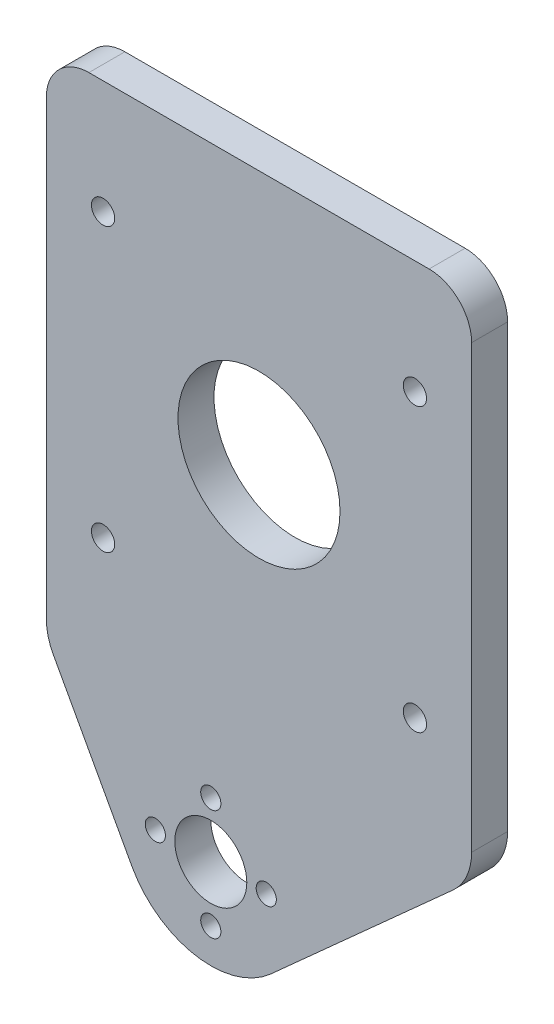
SolidWorks part; units mm, degrees
ref_plane "Front Plane" through (0, 0, 0) normal (0, 0, 1) x (1, 0, 0)
ref_plane "Top Plane" through (0, 0, 0) normal (0, 1, 0) x (1, 0, 0)
ref_plane "Right Plane" through (0, 0, 0) normal (1, 0, 0) x (0, 0, -1)
sketch "Sketch1" plane through (0, 0, 0) normal (0, 0, 1) x (1, 0, 0)
  line L1 (0, 0) -> (304.8, 0)
  line L2 (0, 0) -> (0, 89.8)
  line L3 (0, 89.8) -> (304.8, 89.8)
  line L4 (304.8, 0) -> (304.8, 89.8)
  circle A3 centre (152.4, 44.9) radius 14.2875
  point P7 (152.4, 44.9)
  circle B0 centre (109.4016, 62.8594) radius 2.54
  circle B1 centre (109.3994, 26.9384) radius 2.54
  circle B2 centre (73.4784, 26.9406) radius 2.54
  circle B3 centre (73.4806, 62.8616) radius 2.54
  circle B4 centre (91.44, 44.9) radius 17.145
  circle B5 centre (195.4006, 62.8616) radius 2.54
  circle B6 centre (231.3216, 62.8594) radius 2.54
  circle B7 centre (231.3194, 26.9384) radius 2.54
  circle B8 centre (195.3984, 26.9406) radius 2.54
  circle B9 centre (213.36, 44.9) radius 17.145
  dimension "D3" = 60.96
  dimension "D4" = 60.96
  dimension "D6" = 28.575
  dimension "D1" = 89.8
  dimension "D2" = 304.8
sketch_block_instance "Block1-1"
sketch_block "Block1" parameters "D1"=5.08, "D2"=34.29
sketch_block_instance "Block2-1"
sketch_block "Block2" parameters "D1"=5.08, "D2"=34.29
extrude "Boss-Extrude1" add sketch "Sketch1" along normal blind 6.35
sketch "Sketch2" plane through (0, 0, 6.35) normal (0, 0, 1) x (1, 0, 0)
  line L0 (304.8, 89.8) -> (0, 89.8) construction
  line L1 (114.9, 0) -> (189.9, 0)
  line L2 (114.9, 0) -> (114.9, 89.8)
  line L3 (114.9, 89.8) -> (189.9, 89.8)
  line L4 (189.9, 0) -> (189.9, 89.8)
  line L5 (114.9, 0) -> (189.9, 89.8) construction
  line L6 (114.9, 89.8) -> (189.9, 0) construction
  line L8 (114.9, 89.8) -> (-29.3949, 89.8)
  line L9 (114.9, 89.8) -> (114.9, -10.172)
  line L10 (114.9, -10.172) -> (-29.3949, -10.172)
  line L11 (-29.3949, 89.8) -> (-29.3949, -10.172)
  line L12 (189.9, 89.8) -> (343.3103, 89.8)
  line L13 (189.9, 89.8) -> (189.9, -29.3261)
  line L14 (189.9, -29.3261) -> (343.3103, -29.3261)
  line L15 (343.3103, 89.8) -> (343.3103, -29.3261)
  point P0 (152.4, 44.9)
  line M1 (0, 89.8) -> (0, 0)
  line M2 (0, 0) -> (304.8, 0)
  line M3 (304.8, 0) -> (304.8, 89.8)
  line M4 (304.8, 89.8) -> (0, 89.8)
  circle M6 centre (91.44, 44.9) radius 17.145
  circle M7 centre (109.4016, 62.8594) radius 2.54
  circle M8 centre (109.3994, 26.9384) radius 2.54
  circle M9 centre (73.4784, 26.9406) radius 2.54
  circle M10 centre (73.4806, 62.8616) radius 2.54
  circle M11 centre (213.36, 44.9) radius 17.145
  circle M12 centre (195.4006, 62.8616) radius 2.54
  circle M13 centre (231.3216, 62.8594) radius 2.54
  circle M14 centre (231.3194, 26.9384) radius 2.54
  circle M15 centre (195.3984, 26.9406) radius 2.54
  dimension "D1" = 75
extrude "Cut-Extrude1" cut sketch "Sketch2" against normal blind 10 contours L4 M2 M3 M4 M11 M13 M15 M14 M12 | L2 M2 M4 M1 M6 M8 M10 M9 M7
sketch "Sketch4" plane through (0, 0, 6.35) normal (0, 0, 1) x (1, 0, 0)
  line L0 (114.9, 0) -> (189.9, 0) construction
  line L1 (189.9, 0) -> (154.512, -31.8068)
  line L2 (114.9, 0) -> (129.9651, -27.6048)
  line L3 (189.9, 0) -> (114.9, 0)
  line L4 (189.9, 0) -> (189.9, 89.8) construction
  arc A2 (129.9651, -27.6048) -> (154.512, -31.8068) centre (143.9, -20) ccw
  circle A3 centre (143.9, -20) radius 6.35
  circle A4 centre (143.9, -29.779) radius 1.778
  circle A5 centre (134.121, -20) radius 1.778
  circle A6 centre (153.679, -20) radius 1.778
  circle A7 centre (143.9, -10.221) radius 1.778
  dimension "D1" = 46
  dimension "D3" = 31.75
  dimension "D4" = 20
  dimension "D5" = 12.7
  dimension "D6" = 3.556
  dimension "D7" = 3.556
  dimension "D8" = 3.556
  dimension "D9" = 3.556
extrude "Boss-Extrude2" add sketch "Sketch4" against normal up to surface (6.35 mm away) up to face at (166.6875, 44.9, 0)
fillet "Fillet1" radius 10 2 edges at (114.9, 0, 3.175) (189.9, 0, 3.175)
fillet "Fillet2" radius 7.5 2 edges at (114.9, 89.8, 3.175) (189.9, 89.8, 3.175)
sketch "Sketch7" plane through (0, 0, 6.35) normal (0, 0, 1) x (1, 0, 0)
  line L1 (182.4, 89.8) -> (122.4, 89.8) construction
  line L2 (189.9, 4.4576) -> (189.9, 82.3) construction
  line L3 (114.9, 2.5511) -> (114.9, 82.3) construction
  line L4 (166.6875, 44.9) -> (152.4, 44.9) construction
  circle A0 centre (179.9, 69.8) radius 2.05
  circle A1 centre (124.9, 69.8) radius 2.05
  circle A4 centre (152.4, 44.9) radius 14.2875 construction
  circle A5 centre (124.9, 20) radius 2.05
  circle A6 centre (179.9, 20) radius 2.05
  dimension "D1" = 4.1
  dimension "D2" = 4.1
  dimension "D3" = 20
  dimension "D4" = 20
  dimension "D5" = 10
  dimension "D6" = 10
extrude "Cut-Extrude2" cut sketch "Sketch7" against normal blind 10
